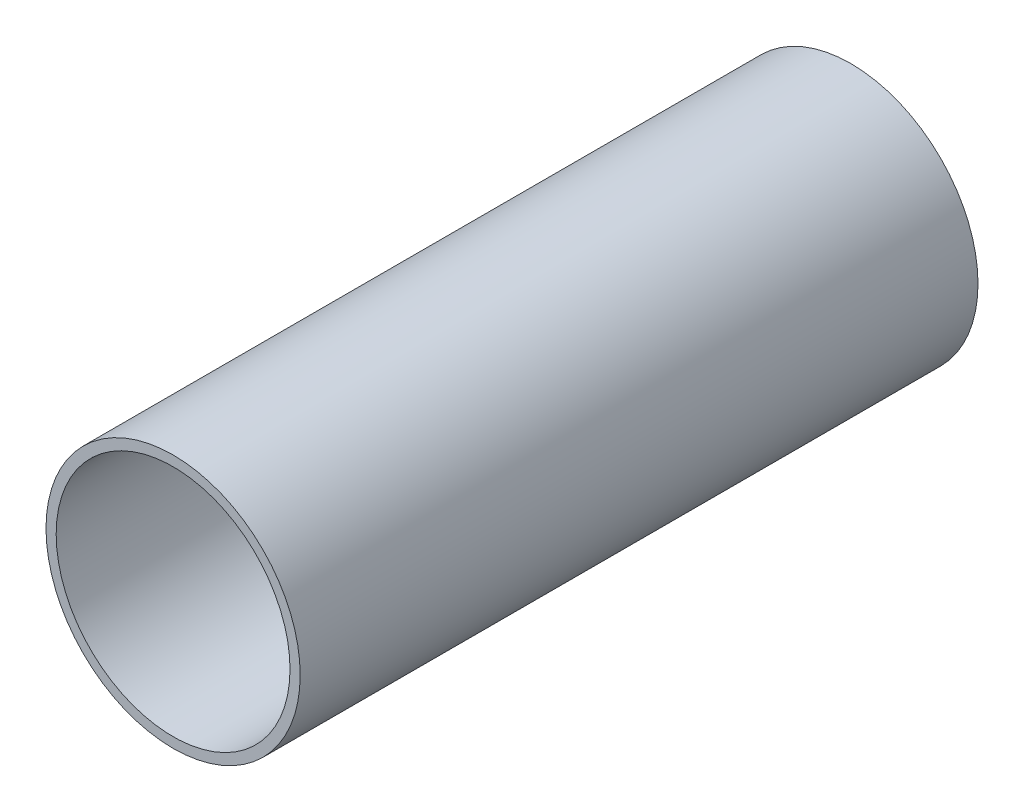
SolidWorks part; units mm, degrees
ref_plane "Ebene vorne" through (0, 0, 0) normal (0, 0, 1) x (1, 0, 0)
ref_plane "Ebene oben" through (0, 0, 0) normal (0, 1, 0) x (1, 0, 0)
ref_plane "Ebene rechts" through (0, 0, 0) normal (1, 0, 0) x (0, 0, -1)
sketch "Skizze1" plane through (0, 0, 0) normal (0, 0, 1) x (1, 0, 0)
  circle A0 centre (0, 0) radius 37.5
  dimension "D1" = 75
extrude "Linear-Austragen-Dünn1" add sketch "Skizze1" along normal blind 200 thin thin type one direction reverse wall 3
